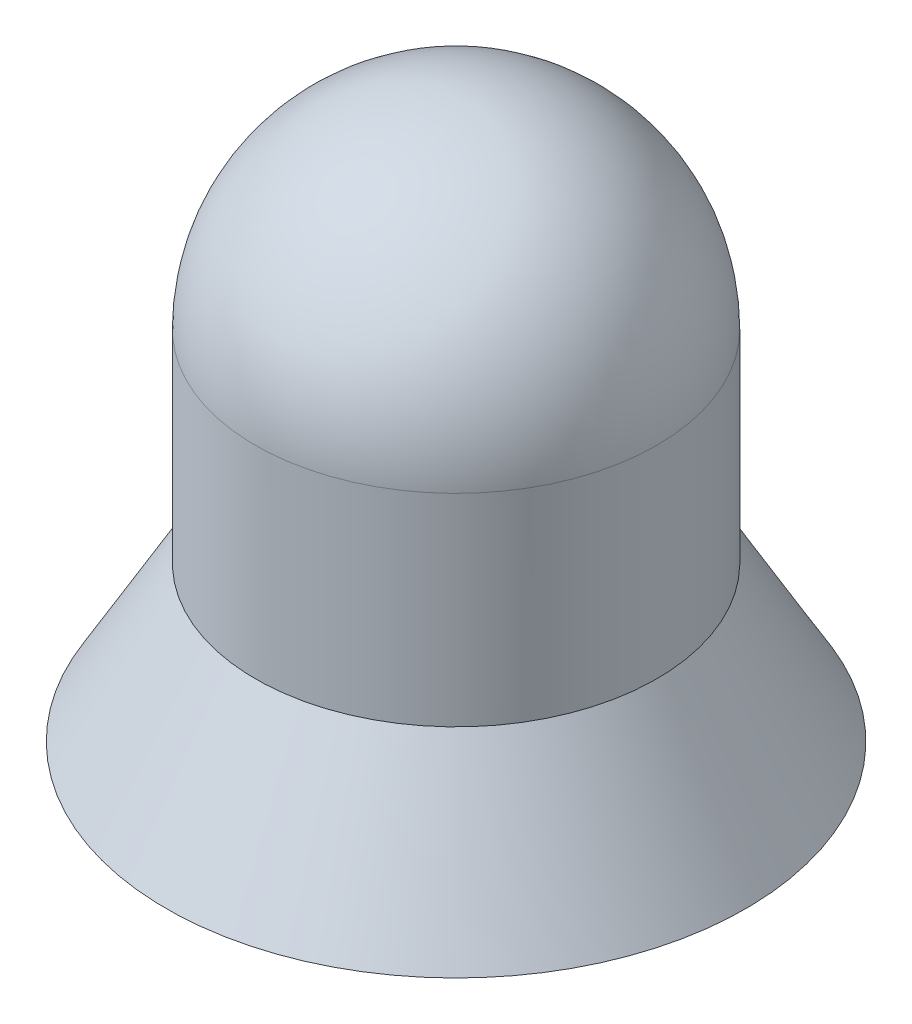
SolidWorks part; units mm, degrees
ref_plane "Front Plane" through (0, 0, 0) normal (0, 0, 1) x (1, 0, 0)
ref_plane "Top Plane" through (0, 0, 0) normal (0, 1, 0) x (1, 0, 0)
ref_plane "Right Plane" through (0, 0, 0) normal (1, 0, 0) x (0, 0, -1)
sketch "Sketch1" plane through (0, 0, 0) normal (0, 0, 1) x (1, 0, 0)
  line L0 (0, 0) -> (0, 2.7702) construction
  line L1 (1.3, 0) -> (0.9, 0.6928)
  line L2 (0.9, 0.6928) -> (0.9, 1.6)
  line L3 (0, 2.5) -> (0, 0)
  line L4 (0, 0) -> (1.3, 0)
  arc A0 (0.9, 1.6) -> (0, 2.5) centre (0, 1.6) ccw
  dimension "D1" = 2.6
  dimension "D4" = 0.9
  dimension "D2" = 2.5
  dimension "D3" = 30
revolve "Revolve1" add sketch "Sketch1" angle 360 about L0
hole_wizard "Ø1.0 (1) Diameter Hole1" positions "Sketch3" profile "Sketch2" hole size "Ø1.0" standard "DIN"
sketch "Sketch3" plane through (0, 0, 0) normal (0, -1, 0) x (-1, 0, 0)
  point P0 (0, 0)
sketch "Sketch2" plane through (0, 0, 0) normal (1, 0, 0) x (0, 0, -1)
  line L0 (0, 0) -> (0, 2.1004)
  line L1 (0, 2.1004) -> (0.5, 1.8)
  line L2 (0.5, 1.8) -> (0.5, 0)
  line L5 (0.5, 0) -> (0, 0)
  line L10 (0, 2.1004) -> (-0.5, 1.8) construction
  line L11 (0, -6.35) -> (0, 107.95) construction
  dimension "Hole Dia." = 1
  dimension "Hole Depth" = 1.8
  dimension "Drill Angle" = 118
